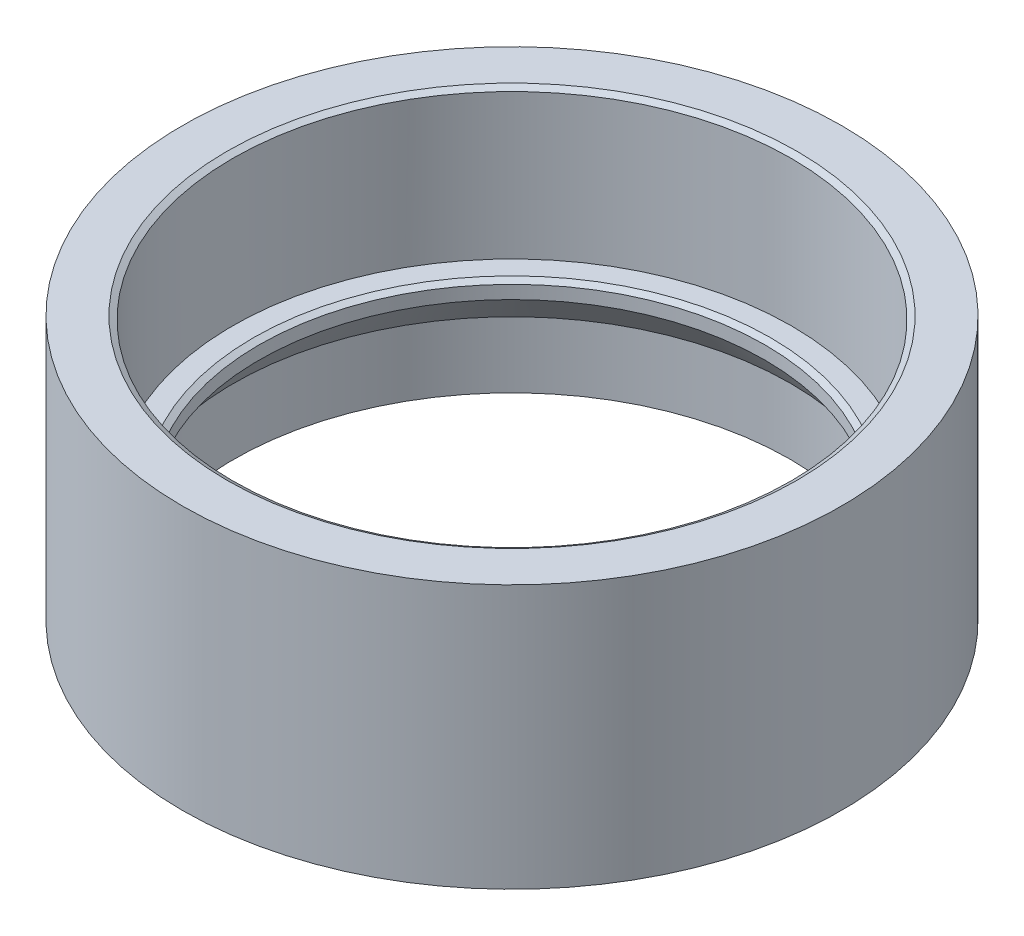
SolidWorks part; units mm, degrees
ref_plane "Front Plane" through (0, 0, 0) normal (0, 0, 1) x (1, 0, 0)
ref_plane "Top Plane" through (0, 0, 0) normal (0, 1, 0) x (1, 0, 0)
ref_plane "Right Plane" through (0, 0, 0) normal (1, 0, 0) x (0, 0, -1)
sketch "Sketch1" plane through (0, 0, 0) normal (0, 0, 1) x (1, 0, 0)
  line L1 (84.75, 80) -> (100, 80)
  line L2 (100, 80) -> (100, 0)
  line L3 (100, 0) -> (95, 0)
  line L4 (76.75, 34.9984) -> (76.75, 29.9984)
  line L5 (0, 0) -> (0, 80) construction
  line L6 (76.75, 34.9984) -> (84.75, 34.9984)
  line L7 (84.75, 34.9984) -> (84.75, 80)
  line L8 (84.5, 0) -> (84.5, 20)
  line L10 (89.9, 0) -> (89.9, 5)
  line L11 (89.9, 5) -> (95, 5)
  line L12 (95, 0) -> (95, 5)
  line L13 (89.9, 0) -> (84.5, 0)
  line L14 (84.5, 20) -> (76.75, 29.9984)
  dimension "D1" = 76.75
  dimension "D2" = 100
  dimension "D3" = 80
  dimension "D4" = 80
  dimension "D5" = 84.75
  dimension "D6" = 37.78
  dimension "D7" = 5.1
  dimension "D8" = 5
  dimension "D9" = 5
  dimension "D10" = 20
  dimension "D11" = 84.5
  dimension "D12" = 5
revolve "Revolve1" add sketch "Sketch1" angle 360 about L5
chamfer "Chamfer2" distance 1 angle 60 2 edges at (0, 34.9984, -76.75) (0, 80, -84.75)
fillet "Fillet1" radius 1 2 edges at (0, 0, -89.9) (0, 0, -95)
